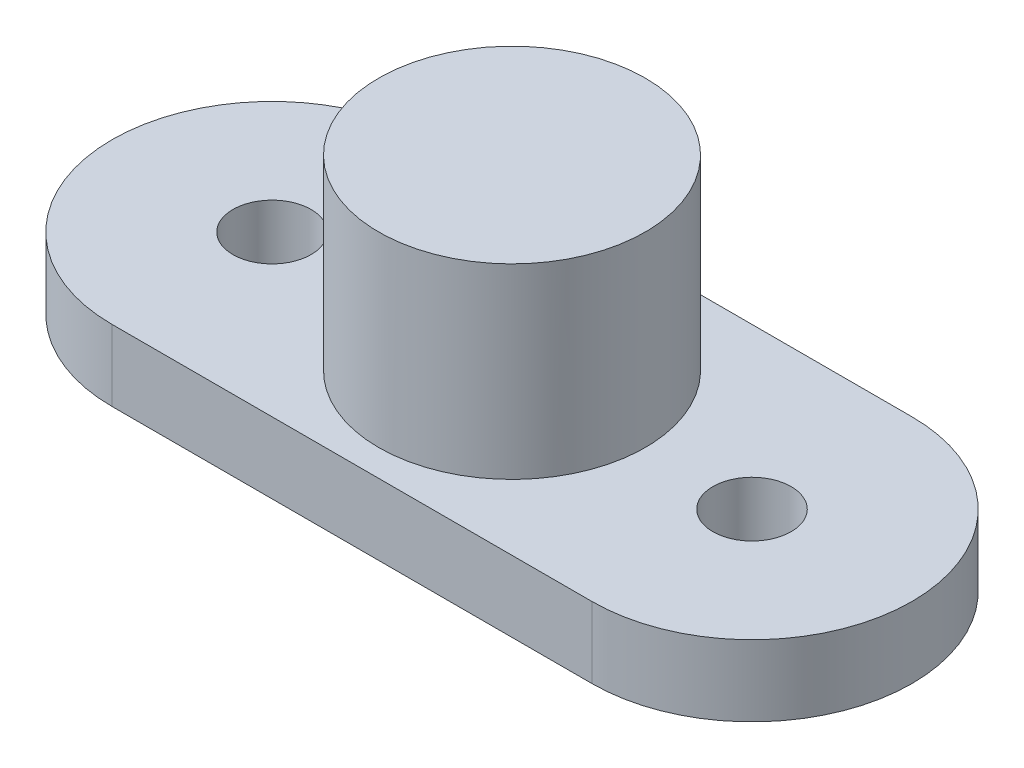
SolidWorks part; units mm, degrees
ref_plane "Front Plane" through (0, 0, 0) normal (0, 0, 1) x (1, 0, 0)
ref_plane "Top Plane" through (0, 0, 0) normal (0, 1, 0) x (1, 0, 0)
ref_plane "Right Plane" through (0, 0, 0) normal (1, 0, 0) x (0, 0, -1)
sketch "Sketch1" plane through (0, 0, 0) normal (0, 1, 0) x (1, 0, 0)
  line L0 (0, 0) -> (6.75, 0)
  line L1 (0, 0) -> (-6.75, 0)
  line L2 (-6.75, 4.4995) -> (6.75, 4.4995)
  line L3 (-6.75, -4.4995) -> (6.75, -4.4995)
  circle A0 centre (-6.75, 0) radius 1.1
  circle A1 centre (6.75, 0) radius 1.1
  arc A2 (6.75, 4.4995) -> (6.75, -4.4995) centre (6.75, 0) cw
  arc A3 (-6.75, 4.4995) -> (-6.75, -4.4995) centre (-6.75, 0) ccw
  circle A6 centre (0, 0) radius 3.75
extrude "Boss-Extrude3" add sketch "Sketch1" along normal blind 2
sketch "Sketch3" plane through (0, 0, 0) normal (0, -1, 0) x (1, 0, 0)
  circle A2 centre (0, 0) radius 3.75
extrude "Boss-Extrude4" add sketch "Sketch3" against normal blind 7.25
